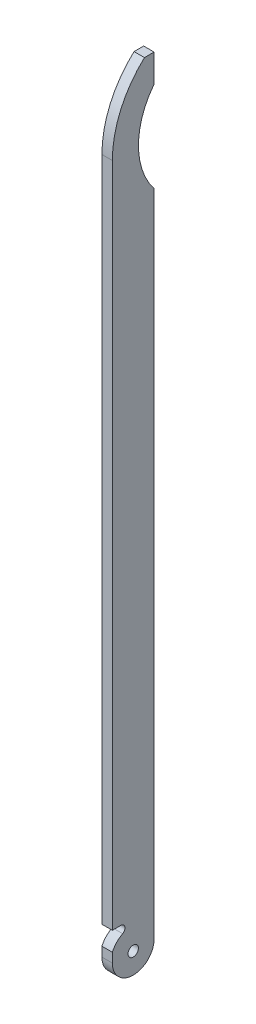
SolidWorks part; units mm, degrees
material "Сплав 2024"
ref_plane "Спереди" through (0, 0, 0) normal (0, 0, 1) x (1, 0, 0)
ref_plane "Сверху" through (0, 0, 0) normal (0, 1, 0) x (1, 0, 0)
ref_plane "Справа" through (0, 0, 0) normal (1, 0, 0) x (0, 0, -1)
sketch "Эскиз1" plane through (0, 0, 0) normal (0, 1, 0) x (1, 0, 0)
  line L1 (0, 0) -> (5, 0)
  line L2 (0, 0) -> (0, -20)
  line L3 (0, -20) -> (5, -20)
  line L4 (5, 0) -> (5, -20)
  dimension "D1" = 20
  dimension "D2" = 5
extrude "Бобышка-Вытянуть1" add sketch "Эскиз1" along normal blind 378
sketch "Эскиз2" plane through (0, 0, 0) normal (-1, 0, 0) x (0, 0, 1)
  line L0 (10, 0) -> (10, 43.6968) construction
  line L1 (0, 0) -> (20, 0) construction
  line L2 (20, 378) -> (20, 0) construction
  line L3 (0, 378) -> (0, 0) construction
  line L4 (-3.9052, 10) -> (23.072, 10) construction
  line L5 (0, 10) -> (0, -2)
  line L6 (0, -2) -> (20, -2)
  line L7 (20, -2) -> (20, 10)
  arc A0 (20, 10) -> (0, 10) centre (10, 10) cw
  dimension "D2" = 10
  dimension "D1" = 10
  dimension "D3" = 2
extrude "Вырез-Вытянуть1" cut sketch "Эскиз2" against normal through all
sketch "Эскиз3" plane through (0, 0, 0) normal (-1, 0, 0) x (0, 0, 1)
  circle A0 centre (10, 10) radius 2.5
  dimension "D1" = 5
extrude "Вырез-Вытянуть2" cut sketch "Эскиз3" against normal through all
sketch "Эскиз4" plane through (0, 0, 0) normal (-1, 0, 0) x (0, 0, 1)
  line L0 (20, 378) -> (20, 10) construction
  line L1 (0, 378) -> (20, 378) construction
  circle A0 centre (-27.5, 343) radius 35
  dimension "D1" = 70
  dimension "D2" = 47.5
  dimension "D3" = 35
extrude "Вырез-Вытянуть3" cut sketch "Эскиз4" against normal through all
sketch "Эскиз5" plane through (0, 0, 0) normal (-1, 0, 0) x (0, 0, 1)
  line L0 (0, 371.3253) -> (0, 392.1343) construction
  line L1 (0, 378) -> (0, 364.6506) construction
  line L4 (20, 378) -> (20, 10) construction
  line L5 (0, 381.7298) -> (20, 378)
  line L6 (20, 378) -> (20, 343)
  arc A2 (9.8214, 313.617) -> (9.8214, 372.383) centre (-27.5, 343) ccw
  arc A3 (20, 343) -> (0, 381.7298) centre (-27.5, 343) ccw
  dimension "D1" = 12.5
extrude "Вырез-Вытянуть4" cut sketch "Эскиз5" against normal through all
sketch "Эскиз6" plane through (5, 0, 0) normal (1, 0, 0) x (0, 0, -1)
  line L0 (-20, 21.56) -> (0, 21.56) construction
  line L1 (-20, 343) -> (-20, 10) construction
  line L2 (0, 321.3494) -> (0, 10) construction
  line L3 (3.9052, 10) -> (-23.072, 10) construction
  line L4 (-16, -2) -> (-16, 28.3112) construction
  line L6 (0, -2) -> (-20, -2) construction
  line L7 (-20, -2) -> (-20, 10) construction
  line L8 (-16, 23.61) -> (-20, 23.61)
  line L10 (-20, 23.61) -> (-20, 19.51)
  line L12 (-20, 19.51) -> (-20, 14.5207)
  arc A0 (-15.0556, 19.7405) -> (-16, 23.61) centre (-16, 21.56) ccw
  arc A1 (-15.0556, 19.7405) -> (-20, 14.5207) centre (-10, 10) ccw
  dimension "D4" = 10.9743
  dimension "D3" = 4.1
  dimension "D1" = 11.56
  dimension "D2" = 4
extrude "Вырез-Вытянуть5" cut sketch "Эскиз6" against normal through all
